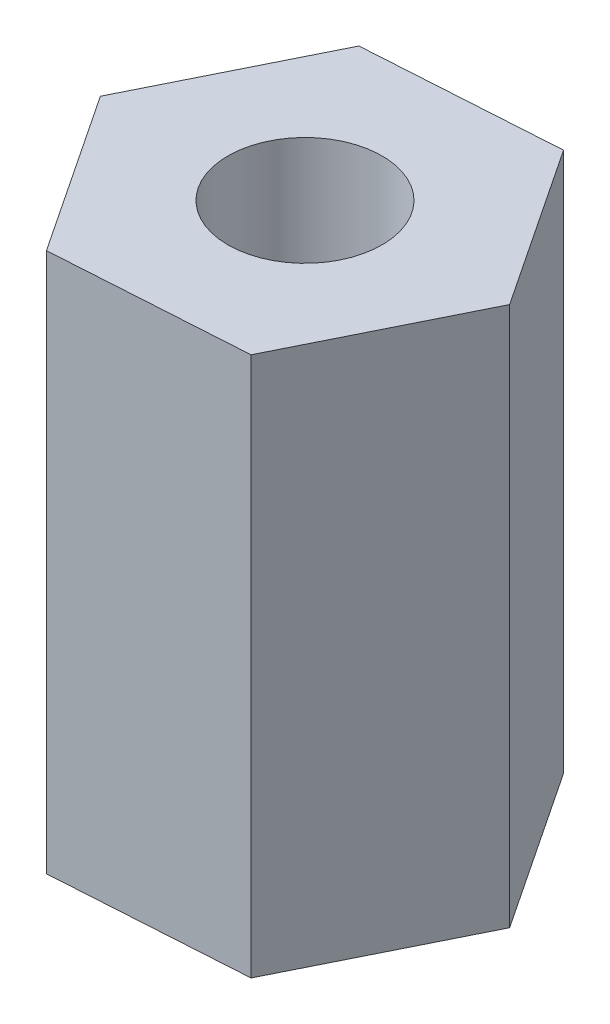
SolidWorks part; units mm, degrees
material "Латунь"
ref_plane "Спереди" through (0, 0, 0) normal (0, 0, 1) x (1, 0, 0)
ref_plane "Сверху" through (0, 0, 0) normal (0, 1, 0) x (1, 0, 0)
ref_plane "Справа" through (0, 0, 0) normal (1, 0, 0) x (0, 0, -1)
sketch "Эскиз1" plane through (0, 0, 0) normal (0, 1, 0) x (1, 0, 0)
  line L1 (-3.3372, -6.7228) -> (4.1535, -6.2515)
  line L2 (4.1535, -6.2515) -> (7.4907, 0.4713)
  line L3 (7.4907, 0.4713) -> (3.3372, 6.7228)
  line L4 (3.3372, 6.7228) -> (-4.1535, 6.2515)
  line L5 (-4.1535, 6.2515) -> (-7.4907, -0.4713)
  line L6 (-7.4907, -0.4713) -> (-3.3372, -6.7228)
  circle A0 centre (0, 0) radius 6.5 construction
  dimension "D1" = 13
extrude "Бобышка-Вытянуть1" add sketch "Эскиз1" along normal blind 21
sketch "Эскиз2" plane through (0, 21, 0) normal (0, 1, 0) x (1, 0, 0)
  circle A0 centre (0, 0) radius 3
  dimension "D1" = 6
extrude "Вырез-Вытянуть1" cut sketch "Эскиз2" against normal through all
